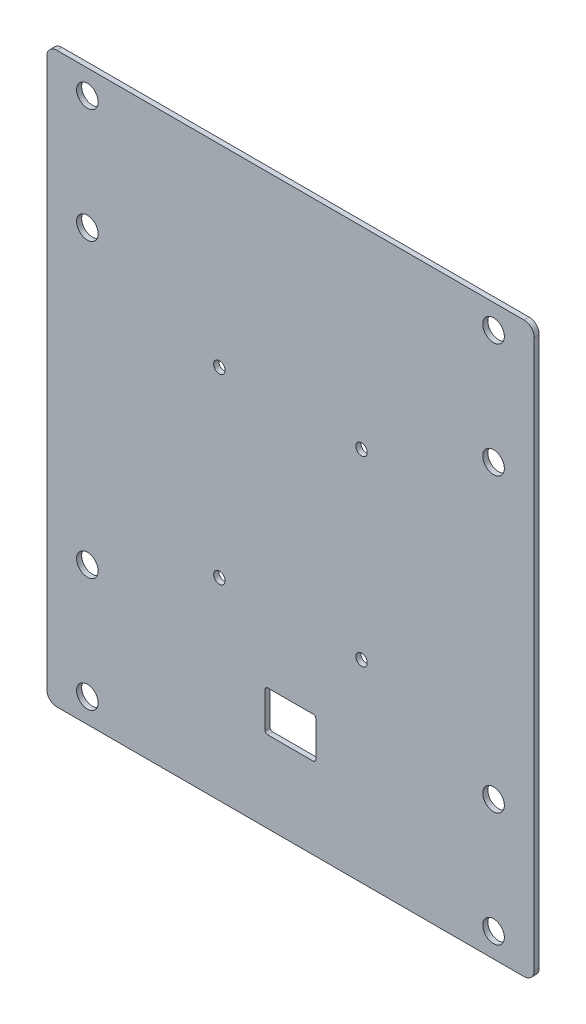
SolidWorks part; units mm, degrees
material "Plain Carbon Steel"
ref_plane "Front Plane" through (0, 0, 0) normal (0, 0, 1) x (1, 0, 0)
ref_plane "Top Plane" through (0, 0, 0) normal (0, 1, 0) x (1, 0, 0)
ref_plane "Right Plane" through (0, 0, 0) normal (1, 0, 0) x (0, 0, -1)
sketch "Sketch1" plane through (0, 0, 0) normal (0, 0, 1) x (1, 0, 0)
  line L1 (-152.4, 177.8) -> (152.4, 177.8)
  line L2 (-152.4, 177.8) -> (-152.4, -177.8)
  line L3 (-152.4, -177.8) -> (152.4, -177.8)
  line L4 (152.4, 177.8) -> (152.4, -177.8)
  line L5 (-152.4, 177.8) -> (152.4, -177.8) construction
  line L6 (-152.4, -177.8) -> (152.4, 177.8) construction
  point P0 (0, 0)
  dimension "D1" = 304.8
  dimension "D2" = 355.6
extrude "Boss-Extrude1" add sketch "Sketch1" along normal blind 3.175
sketch "Sketch2" plane through (0, 0, 3.175) normal (0, 0, 1) x (1, 0, 0)
  line L0 (-127, -91.2813) -> (127, -91.2813) construction
  line L1 (127, 162.7187) -> (-127, 162.7187)
  line L2 (127, 162.7187) -> (127, -162.7187)
  line L3 (127, -162.7187) -> (-127, -162.7188)
  line L4 (-127, 162.7187) -> (-127, -162.7188)
  line L5 (127, 162.7187) -> (-127, -162.7188) construction
  line L6 (127, -162.7187) -> (-127, 162.7187) construction
  line L7 (-152.4, 177.8) -> (-152.4, -177.8) construction
  line L8 (-127, 91.2812) -> (127, 91.2812) construction
  line L10 (0, 162.7187) -> (0, 91.2812) construction
  line L11 (0, 91.2812) -> (0, 0) construction
  line L12 (0, 0) -> (0, -91.2812) construction
  line L13 (0, -91.2812) -> (0, -162.7188) construction
  line L14 (15.875, 101.6) -> (-15.875, 101.6)
  line L15 (15.875, 101.6) -> (15.875, -101.6)
  line L16 (15.875, -101.6) -> (-15.875, -101.6)
  line L17 (-15.875, 101.6) -> (-15.875, -101.6)
  line L18 (15.875, -101.6) -> (-15.875, -101.6)
  line L19 (15.875, -101.6) -> (15.875, -127)
  line L20 (15.875, -127) -> (-15.875, -127)
  line L21 (-15.875, -101.6) -> (-15.875, -127)
  point P0 (0, 0)
  point P17 (0, -127)
  point P22 (0, 101.6)
  point P25 (-15.875, 0)
  dimension "D1" = 25.4
  dimension "D2" = 71.4375
  dimension "D3" = 127
  dimension "D4" = 203.2
  dimension "D5" = 31.75
  dimension "D6" = 25.4
hole_wizard "17/32 (0.53125) Diameter Hole1" positions "Sketch3" profile "Sketch4" hole size "17/32" standard "ANSI Inch" end condition through all
sketch "Sketch3" plane through (0, 0, 3.175) normal (0, 0, 1) x (1, 0, 0)
  point P0 (-127, 162.7187)
  point P3 (-127, 91.2812)
  point P6 (-127, -91.2813)
  point P9 (-127, -162.7188)
  point P12 (127, -162.7187)
  point P15 (127, -91.2813)
  point P18 (127, 91.2812)
  point P21 (127, 162.7187)
sketch "Sketch4" plane through (-127, 162.7187, 3.175) normal (1, 0, 0) x (0, -1, 0)
  line L0 (0, 0) -> (0, 3.175)
  line L1 (0, 3.175) -> (6.7469, 3.175)
  line L2 (6.7469, 3.175) -> (6.7469, 0)
  line L5 (6.7469, 0) -> (0, 0)
  line L11 (0, -6.35) -> (0, 107.95) construction
  dimension "Thru Hole Dia." = 13.4937
  dimension "Thru Hole Depth" = 3.175
fillet "Fillet1" radius 6.35 4 edges at (152.4, -177.8, 1.5875) (-152.4, -177.8, 1.5875) (152.4, 177.8, 1.5875) (-152.4, 177.8, 1.5875)
sketch "Sketch7" plane through (0, 0, 0) normal (0, 0, -1) x (-1, 0, 0)
  line L0 (-127, -162.7187) -> (127, 162.7187) construction
  line L1 (44.45, 56.9516) -> (-44.45, 56.9516)
  line L2 (44.45, 56.9516) -> (44.45, -56.9516)
  line L3 (44.45, -56.9516) -> (-44.45, -56.9516)
  line L4 (-44.45, 56.9516) -> (-44.45, -56.9516)
  line L5 (44.45, 56.9516) -> (-44.45, -56.9516) construction
  line L6 (44.45, -56.9516) -> (-44.45, 56.9516) construction
  point P0 (0, 0)
  dimension "D1" = 88.9
hole_wizard "1/4 Clearance Hole1" positions "Sketch8" profile "Sketch9" hole size "1/4" standard "ANSI Inch" end condition through all
sketch "Sketch8" plane through (0, 0, 0) normal (0, 0, -1) x (-1, 0, 0)
  point P0 (-44.45, 56.9516)
  point P3 (-44.45, -56.9516)
  point P6 (44.45, 56.9516)
  point P9 (44.45, -56.9516)
sketch "Sketch9" plane through (44.45, 56.9516, 0) normal (1, 0, 0) x (0, 1, 0)
  line L0 (0, 0) -> (0, 3.175)
  line L1 (0, 3.175) -> (3.5712, 3.175)
  line L2 (3.5712, 3.175) -> (3.5712, 0)
  line L5 (3.5712, 0) -> (0, 0)
  line L11 (0, -6.35) -> (0, 107.95) construction
  dimension "Thru Hole Dia." = 7.1425
  dimension "Thru Hole Depth" = 3.175
extrude "Cut-Extrude1" cut sketch "Sketch2" against normal through all contours L16 L21 L20 L19
sketch "Sketch10" plane through (0, 0, 0) normal (0, 0, -1) x (-1, 0, 0)
  line L0 (-146.05, 177.8) -> (146.05, 177.8) construction
  line L1 (12.7, 101.6) -> (-12.7, 101.6)
  line L2 (12.7, 101.6) -> (12.7, -82.55)
  line L3 (12.7, -82.55) -> (-12.7, -82.55)
  line L4 (-12.7, 101.6) -> (-12.7, -82.55)
  point P6 (0, -82.55)
  dimension "D1" = 25.4
  dimension "D2" = 184.15
  dimension "D3" = 76.2
fillet "Fillet2" radius 1.5875 4 edges at (15.875, -127, 1.5875) (-15.875, -127, 1.5875) (-15.875, -101.6, 1.5875) (15.875, -101.6, 1.5875)
